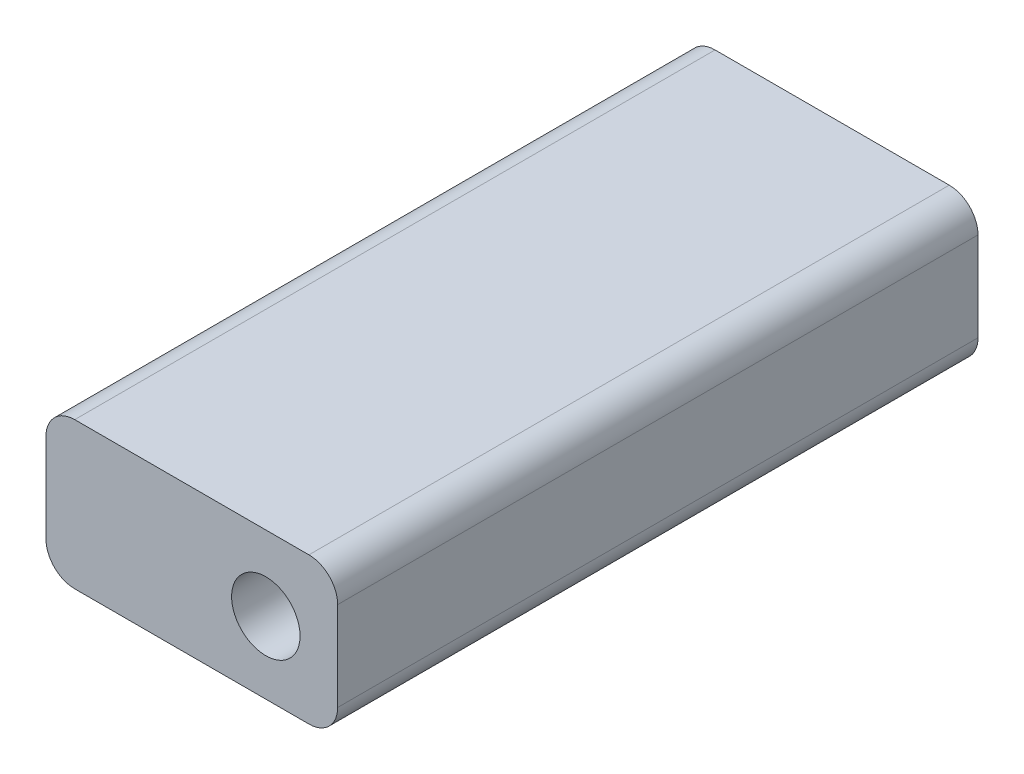
SolidWorks part; units mm, degrees
material "ABS"
ref_plane "X-Y Datum" through (0, 0, 0) normal (0, 0, 1) x (1, 0, 0)
ref_plane "X-Z Datum" through (0, 0, 0) normal (0, 1, 0) x (1, 0, 0)
ref_plane "Y-Z Datum" through (0, 0, 0) normal (1, 0, 0) x (0, 0, -1)
sketch "Sketch1" plane through (0, 0, 0) normal (0, 0, 1) x (1, 0, 0)
  line L1 (-19.43, 91.526) -> (6.35, 91.526)
  line L2 (-19.43, 91.526) -> (-19.43, 78.572)
  line L3 (-19.43, 78.572) -> (6.35, 78.572)
  line L4 (6.35, 91.526) -> (6.35, 78.572)
  circle A0 centre (0, 84.922) radius 6.35 construction
  circle A1 centre (0, 84.922) radius 3.025
extrude "Boss-Extrude1" add sketch "Sketch1" along normal blind 56.5988
sketch "Sketch2" plane through (0, 78.572, 0) normal (0, -1, 0) x (1, 0, 0)
  line L0 (-19.43, 0) -> (6.35, 0) construction
  line L1 (-19.43, 56.5988) -> (-14.35, 56.5988)
  line L2 (-19.43, 56.5988) -> (-19.43, 0)
  line L3 (-19.43, 0) -> (-14.35, 0)
  line L4 (-14.35, 56.5988) -> (-14.35, 0)
extrude "Boss-Extrude2" [suppressed] add sketch "Sketch2" along normal blind 22.6162
sketch "Sketch3" [suppressed] plane through (-14.35, 0, 0) normal (1, 0, 0) x (0, 0, -1)
  line L0 (0, 55.9558) -> (0, 78.572) construction
  line L1 (-56.5988, 55.9558) -> (0, 55.9558)
  line L2 (-56.5988, 55.9558) -> (-56.5988, 61.0358)
  line L3 (-56.5988, 61.0358) -> (0, 61.0358)
  line L4 (0, 55.9558) -> (0, 61.0358)
extrude "Boss-Extrude3" [suppressed] add sketch "Sketch3" along normal blind 17.2695
sketch "Sketch4" [suppressed] plane through (0, 55.9558, 0) normal (0, -1, 0) x (1, 0, 0)
  line L1 (2.9195, 56.5988) -> (2.9195, 0)
  line L4 (9.2695, 56.5988) -> (9.2695, 50.2488) construction
  line L5 (-32.13, 28.2994) -> (-42.0441, 28.2994) construction
  line L6 (2.9195, 56.5988) -> (15.6195, 56.5988)
  line L7 (15.6195, 56.5988) -> (15.6195, 0)
  line L8 (15.6195, 0) -> (2.9195, 0)
  circle A1 centre (9.2695, 50.2488) radius 6.35 construction
  circle A2 centre (9.2695, 50.2488) radius 3.025
  circle A3 centre (9.2695, 6.35) radius 3.025
extrude "Boss-Extrude4" [suppressed] add sketch "Sketch4" against normal up to surface (5.08 mm away)
fillet "Fillet1" [suppressed] radius 2.54
fillet "Fillet2" radius 2.54 4 edges at (-19.43, 91.526, 28.2994) (6.35, 91.526, 28.2994) (6.35, 78.572, 28.2994) (-19.43, 78.572, 28.2994)
sketch "Sketch5" [suppressed] plane through (0, 61.0358, 0) normal (0, 1, 0) x (1, 0, 0)
  circle A0 centre (9.2695, -6.35) radius 6.35
  circle A1 centre (9.2695, -50.2488) radius 6.35
  circle A2 centre (9.2695, -6.35) radius 3.025
  circle A3 centre (9.2695, -50.2488) radius 2.625
extrude "Boss-Extrude5" [suppressed] add sketch "Sketch5" along normal blind 10 and the other way through all
